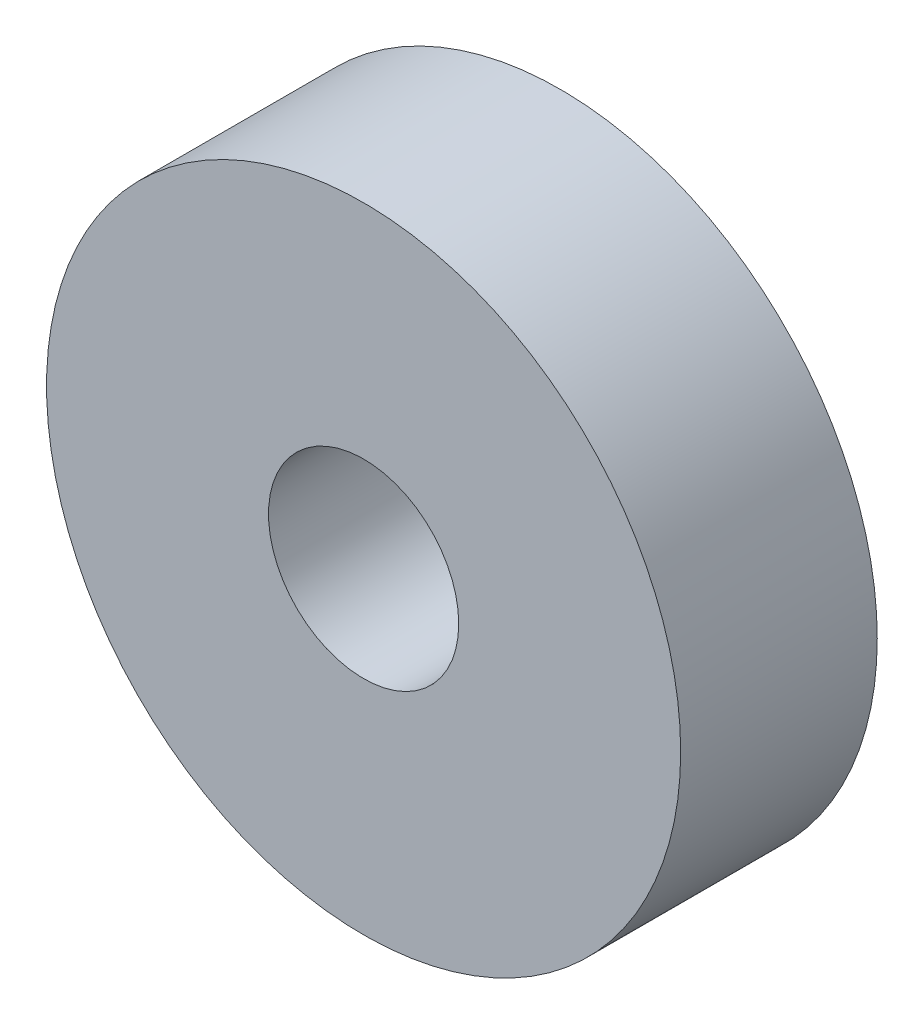
SolidWorks part; units mm, degrees
ref_plane "Front Plane" through (0, 0, 0) normal (0, 0, 1) x (1, 0, 0)
ref_plane "Top Plane" through (0, 0, 0) normal (0, 1, 0) x (1, 0, 0)
ref_plane "Right Plane" through (0, 0, 0) normal (1, 0, 0) x (0, 0, -1)
sketch "Sketch1" plane through (0, 0, 0) normal (0, 0, 1) x (1, 0, 0)
  circle A0 centre (0, 0) radius 50
  dimension "D1" = 100
extrude "Boss-Extrude1" add sketch "Sketch1" along normal blind 31
sketch "Sketch2" plane through (0, 0, 31) normal (0, 0, 1) x (1, 0, 0)
  circle A0 centre (0, 0) radius 15
  dimension "D1" = 30
extrude "Cut-Extrude1" cut sketch "Sketch2" against normal through all
ref_point "Point1"
